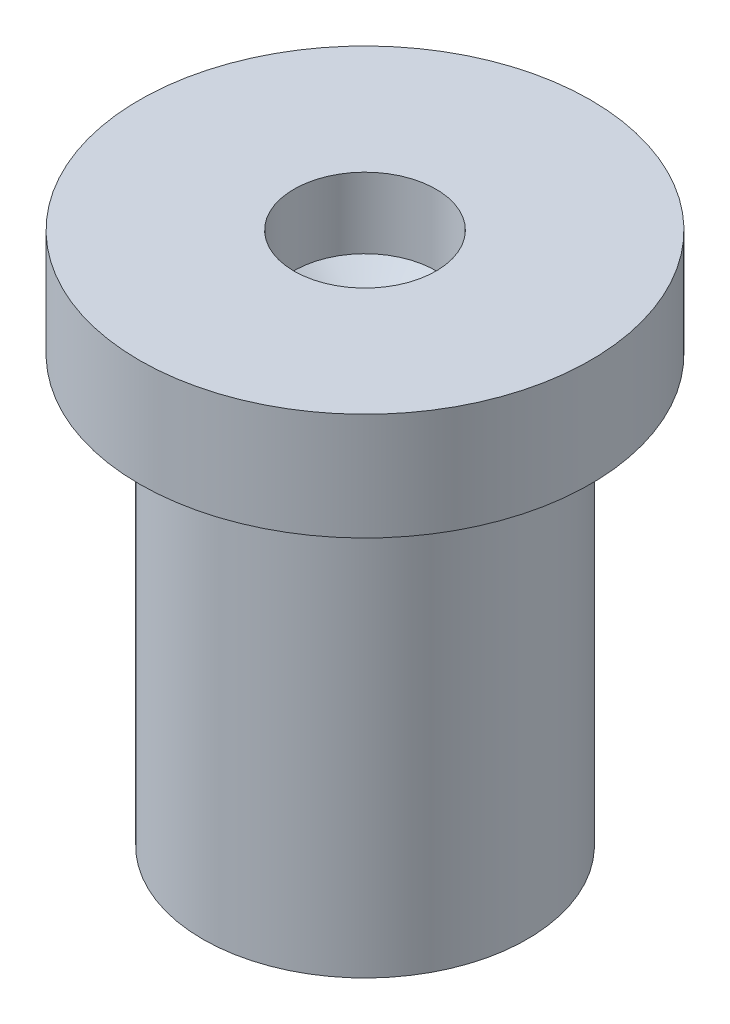
SolidWorks part; units mm, degrees
ref_plane "Front Plane" through (0, 0, 0) normal (0, 0, 1) x (1, 0, 0)
ref_plane "Top Plane" through (0, 0, 0) normal (0, 1, 0) x (1, 0, 0)
ref_plane "Right Plane" through (0, 0, 0) normal (1, 0, 0) x (0, 0, -1)
sketch "Sketch2" plane through (0, 0, 0) normal (0, 0, 1) x (1, 0, 0)
  line L0 (0, 7.0484) -> (0, -5.5) construction
  line L1 (0, -4.6935) -> (4, -4.6935)
  line L2 (4, -4.6935) -> (4, 5.8065)
  line L3 (4, 5.8065) -> (5.5616, 5.8065)
  line L4 (5.5616, 5.8065) -> (5.5616, 8.4494)
  line L5 (5.5616, 8.4494) -> (1.751, 8.4494)
  line L6 (1.751, 8.4494) -> (1.751, 6.7076)
  line L7 (1.751, 6.7076) -> (0, 5.5304)
  line L8 (0, -4.6935) -> (0, 5.5304)
  point P5 (1.0256, 6.2199)
  point P12 (0, 5.3833)
  point P13 (0, 5.5304)
  dimension "D1" = 8
  dimension "D2" = 10.5
revolve "Revolve1" add sketch "Sketch2" angle 360 about L0
